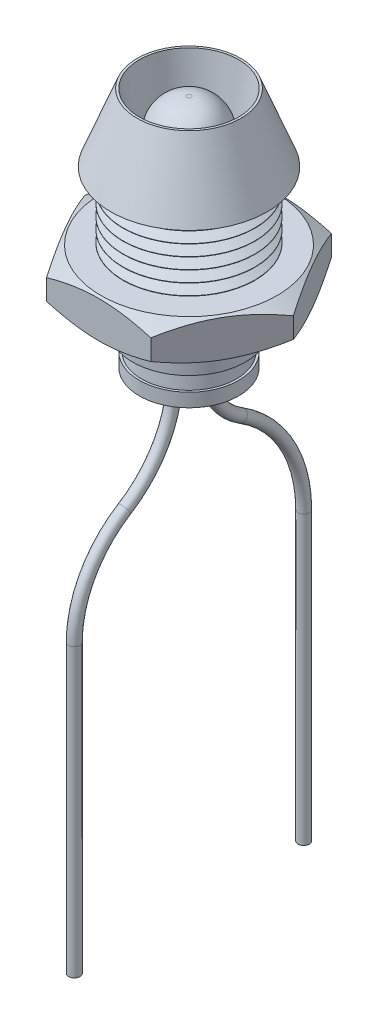
SolidWorks part; units mm, degrees
other "Nut"
other "Tip"
other "Wire LED"
other "LED Light"
other "Plastic Insert"
material "Plain Carbon Steel"
ref_plane "Front Plane" through (0, 0, 0) normal (0, 0, 1) x (1, 0, 0)
ref_plane "Top Plane" through (0, 0, 0) normal (0, 1, 0) x (1, 0, 0)
ref_plane "Right Plane" through (0, 0, 0) normal (1, 0, 0) x (0, 0, -1)
sketch "Sketch1" plane through (0, 0, 0) normal (0, 0, 1) x (1, 0, 0)
  line L0 (0, 0) -> (0, 9.25)
  line L1 (0, 0) -> (2.5, 0)
  line L2 (2.92, 0.6) -> (2.92, 6.25)
  line L3 (0, 9.25) -> (2.3, 9.25)
  line L4 (2.92, 6.25) -> (3.47, 6.25)
  line L5 (3.47, 6.25) -> (2.3, 9.25)
  line L6 (2.5, 0) -> (2.5, 0.6)
  line L7 (2.5, 0.6) -> (2.92, 0.6)
  dimension "D1" = 9.25
  dimension "D2" = 2.92
  dimension "D3" = 2.3
  dimension "D4" = 3.47
  dimension "D5" = 3
  dimension "D6" = 2.5
  dimension "D7" = 6.25
  dimension "D8" = 0.6
revolve "Revolve1" add sketch "Sketch1" angle 360 about L0
sketch "Sketch6" plane through (0, 0, 0) normal (0, 0, 1) x (1, 0, 0)
  line L0 (0, 0) -> (0, 9.25)
  line L1 (2.3, 9.25) -> (-2.3, 9.25) construction
  line L2 (0, 0) -> (2.05, 0)
  line L3 (2.05, 0) -> (2.05, 5.8)
  line L4 (2.05, 5.8) -> (1.75, 5.8)
  line L5 (1.75, 5.8) -> (2.2, 9.25)
  line L6 (2.2, 9.25) -> (0, 9.25)
  line L7 (1.75, 5.8) -> (0, 5.8) construction
  dimension "D1" = 2.05
  dimension "D2" = 5.8
  dimension "D3" = 2.2
  dimension "D4" = 1.75
revolve "Cut-Revolve2" cut sketch "Sketch6" angle 360 about L0
sketch "Sketch5" plane through (0, 0, 0) normal (0, 0, 1) x (1, 0, 0)
  line L0 (0, 0) -> (0, 0.6) construction
  line L1 (-2.5, 0.6) -> (2.5, 0.6) construction
  line L2 (0, 0.6) -> (2.5, 0.6) construction
  line L3 (2.5, 0.6) -> (2.933, 0.6) construction
  line L4 (2.933, 0.6) -> (3.433, 0.6) construction
  line L5 (3.433, 0.85) -> (3.433, 0.35)
  line L6 (2.933, 0.85) -> (2.933, 0.35) construction
  line L7 (3.433, 0.85) -> (2.933, 0.85)
  line L8 (2.933, 0.85) -> (2.5, 0.6)
  line L9 (2.5, 0.6) -> (2.933, 0.35)
  line L10 (2.933, 0.35) -> (3.433, 0.35)
  line L11 (2.5, 0) -> (2.5, 0.6) construction
  point P12 (2.959, 0.6)
  point P13 (2.5, 0.6)
  dimension "D1" = 0.5
  dimension "D2" = 60
revolve "Cut-Revolve1" cut sketch "Sketch5" angle 360 about L0
pattern_linear "LPattern1" count 11 spacing 0.5 along (0, 1, 0) of "Cut-Revolve1"
ref_plane "GAP DISTANCE" through (0, 3.25, 0) normal (0, -1, 0) x (-1, 0, 0)
sketch "Sketch7" plane through (0, 3.25, 0) normal (0, -1, 0) x (-1, 0, 0)
  line L1 (-4.6188, 0) -> (-2.3094, -4)
  line L2 (-2.3094, -4) -> (2.3094, -4)
  line L3 (2.3094, -4) -> (4.6188, 0)
  line L4 (4.6188, 0) -> (2.3094, 4)
  line L5 (2.3094, 4) -> (-2.3094, 4)
  line L6 (-2.3094, 4) -> (-4.6188, 0)
  circle A0 centre (0, 0) radius 4 construction
  circle A1 centre (0, 0) radius 2.6
  dimension "D1" = 8
  dimension "D2" = 5.2
extrude "Boss-Extrude1" add sketch "Sketch7" along normal blind 1.74 separate body
sketch "Sketch8" plane through (0, 0, 0) normal (0, 0, 1) x (1, 0, 0)
  line L0 (0, 0) -> (0, 1.51) construction
  line L1 (2.3094, 1.51) -> (-2.3094, 1.51) construction
  line L2 (0, 1.51) -> (0, 3.25) construction
  line L3 (2.3094, 3.25) -> (-2.3094, 3.25) construction
  line L4 (0, 3.25) -> (3.9, 3.25) construction
  line L5 (4.6188, 3.25) -> (2.3094, 3.25) construction
  line L6 (3.9, 3.25) -> (3.9, 1.51) construction
  line L7 (4.6188, 1.51) -> (2.3094, 1.51) construction
  line L8 (3.9, 1.51) -> (0, 1.51) construction
  line L9 (3.9, 3.25) -> (4.6188, 3.25)
  line L10 (4.6188, 3.25) -> (4.6188, 2.835)
  line L11 (4.6188, 1.51) -> (4.6188, 3.25) construction
  line L12 (4.6188, 2.835) -> (3.9, 3.25)
  line L13 (3.9, 1.51) -> (4.6188, 1.51)
  line L14 (4.6188, 1.51) -> (4.6188, 1.925)
  line L15 (4.6188, 1.925) -> (3.9, 1.51)
  point P5 (4.6188, 2.6837)
  point P23 (4.6188, 1.441)
  dimension "D1" = 3.9
  dimension "D2" = 30
revolve "Cut-Revolve3" cut sketch "Sketch8" angle 360 about L2
sketch "Sketch11" plane through (0, 0, 0) normal (0, 0, 1) x (1, 0, 0)
  line L0 (0, 3.55) -> (0, -1.45)
  line L1 (0, -1.45) -> (2.2, -1.45)
  line L2 (0, 3.55) -> (1.75, 3.55)
  line L4 (2.2, -1.45) -> (2.2, -0.85)
  line L5 (2.2, -0.85) -> (2.1, -0.85)
  line L6 (2.1, -0.85) -> (1.75, 3.55)
  line L7 (0, 3.55) -> (0, 9.25) construction
  line L8 (2.3, 9.25) -> (-2.3, 9.25) construction
  dimension "D1" = 0.1
  dimension "D2" = 2.2
  dimension "D3" = 1.75
  dimension "D4" = 5
  dimension "D5" = 0.6
  dimension "D6" = 10.7
revolve "Revolve2" add sketch "Sketch11" angle 360 about L7
sketch "Sketch12" plane through (0, 3.55, 0) normal (0, 1, 0) x (1, 0, 0)
  circle A0 centre (0, 0) radius 1.5
  dimension "D1" = 3
extrude "Cut-Extrude5" cut sketch "Sketch12" against normal offset from surface (4.4 mm away) 0.6 up to face at (0, -1.45, -2.2)
sketch "Sketch13" plane through (0, -0.85, 0) normal (0, 1, 0) x (1, 0, 0)
  line L0 (0, 0.635) -> (0, -0.635) construction
  line L2 (-0.4, 1.035) -> (0.4, 1.035)
  line L3 (-0.4, 1.035) -> (-0.4, 0.235)
  line L4 (-0.4, 0.235) -> (0.4, 0.235)
  line L5 (0.4, 1.035) -> (0.4, 0.235)
  line L6 (-0.4, 1.035) -> (0.4, 0.235) construction
  line L7 (-0.4, 0.235) -> (0.4, 1.035) construction
  line L8 (-0.4, -0.235) -> (0.4, -0.235)
  line L9 (-0.4, -0.235) -> (-0.4, -1.035)
  line L10 (-0.4, -1.035) -> (0.4, -1.035)
  line L11 (0.4, -0.235) -> (0.4, -1.035)
  line L12 (-0.4, -0.235) -> (0.4, -1.035) construction
  line L13 (-0.4, -1.035) -> (0.4, -0.235) construction
  dimension "D1" = 1.27
  dimension "D2" = 0.8
extrude "Cut-Extrude6" cut sketch "Sketch13" against normal up to surface (0.6 mm away) up to face at (0, -1.45, -2.2)
sketch "Sketch14" plane through (0, -1.45, 0) normal (0, -1, 0) x (1, 0, 0)
  line L0 (0, 1.035) -> (0, 0.235) construction
  line L1 (-0.4, 1.035) -> (0.4, 1.035) construction
  line L2 (0.4, 0.235) -> (-0.4, 0.235) construction
  line L3 (0, -0.235) -> (0, -1.035) construction
  line L4 (-0.4, -0.235) -> (0.4, -0.235) construction
  line L5 (0.4, -1.035) -> (-0.4, -1.035) construction
  circle A0 centre (0, -0.635) radius 0.6
  circle A1 centre (0, 0.635) radius 0.6
  dimension "D1" = 1.2
extrude "Cut-Extrude7" cut sketch "Sketch14" against normal blind 0.1
sketch "Sketch21" plane through (0, -1.45, 0) normal (0, -1, 0) x (1, 0, 0)
  line L0 (0, 0) -> (0, 1.4) construction
  line L1 (0, 0) -> (0, -2) construction
  line L2 (-1.25, -2) -> (1.25, -2) construction
  line L3 (-1.25, 1.4) -> (1.25, 1.4) construction
  text T0 "A" font "Calibri" height 0.6
  text T1 "C" font "Calibri" height 0.6
  dimension "D1" = 2
  dimension "D2" = 1.4
extrude "Cut-Extrude9" cut sketch "Sketch21" against normal blind 0.01
sketch "Sketch15" plane through (0, 0, 0) normal (0, 0, 1) x (1, 0, 0)
  line L0 (0, 0) -> (0, 3.55) construction
  line L1 (1.75, 3.55) -> (-1.75, 3.55) construction
  line L2 (0, 3.55) -> (0, 8.95)
  line L3 (0, 3.55) -> (1.89, 3.55)
  line L4 (1.89, 3.55) -> (1.89, 4.75)
  line L5 (1.89, 4.75) -> (1.5, 4.75)
  line L6 (1.5, 4.75) -> (1.5, 5.05)
  line L8 (0.1, 8.95) -> (0, 8.95)
  line L9 (1.5, 5.05) -> (1.5, 7.55) construction
  line L10 (1.5, 7.55) -> (1.5, 8.95) construction
  line L11 (1.5, 8.95) -> (0.1, 8.95) construction
  line L12 (1.5, 7.55) -> (1.47, 7.55) construction
  line L13 (1.5, 4.75) -> (0, 4.75) construction
  line L14 (1.47, 7.55) -> (0, 7.55) construction
  arc A0 (1.5, 5.05) -> (1.4676, 7.6464) centre (-102.6817, 5.05) ccw
  arc A1 (0.1, 8.95) -> (1.4616, 7.7345) centre (0.1, 7.5797) cw
  arc A2 (1.4616, 7.7345) -> (1.4676, 7.6464) centre (0.468, 7.6215) cw
  dimension "D1" = 1.5
  dimension "D7" = 0.1
  dimension "D9" = 1
  dimension "D2" = 1.89
  dimension "D3" = 1.2
  dimension "D4" = 5.4
  dimension "D5" = 1.47
  dimension "D6" = 1.5
  dimension "D8" = 4
revolve "Revolve3" add sketch "Sketch15" angle 360 about L2
sketch "Sketch17" plane through (0, 4.75, 0) normal (0, 1, 0) x (1, 0, 0)
  line L0 (0, 0) -> (0, 1.53) construction
  line L1 (-1.1096, 1.53) -> (1.1096, 1.53)
  circle A0 centre (0, 0) radius 1.89 construction
  arc A1 (1.1096, 1.53) -> (-1.1096, 1.53) centre (0, 0) ccw
  point P3 (0.707, 2.52)
  point P4 (0, 1.9022)
  point P5 (0, 2.1105)
  point P7 (0, 1.5432)
  point P9 (1.1905, 1.5275)
  dimension "D1" = 1.53
extrude "Cut-Extrude8" cut sketch "Sketch17" against normal up to surface (1.2 mm away) up to face at (0, 3.55, -1.89)
sketch "Sketch Wire Path" plane through (0, 0, 0) normal (1, 0, 0) x (0, 0, -1)
  line L0 (0, 0) -> (0, 3.55) construction
  line L1 (-0.635, -1.45) -> (0.635, -1.45) construction
  line L2 (-1.89, 3.55) -> (1.53, 3.55) construction
  line L3 (0, 3.55) -> (0, 4.75) construction
  line L4 (1.53, 4.75) -> (-1.89, 4.75) construction
  line L5 (-0.635, 4.15) -> (0, 4.15)
  line L6 (-0.635, 4.15) -> (-0.635, -1.45)
  line L7 (0.635, 4.15) -> (0.635, -1.45)
  line L8 (-0.635, -1.45) -> (-0.635, -5.45) construction
  line L9 (-0.635, -5.45) -> (-2.8575, -5.45) construction
  line L10 (-2.8575, -5.45) -> (-5.08, -5.45) construction
  line L11 (-5.08, -5.45) -> (-5.08, -9.45) construction
  line L12 (0.635, -1.45) -> (0.635, -4.45) construction
  line L13 (0.635, -4.45) -> (2.3019, -4.45) construction
  line L14 (2.3019, -4.45) -> (5.08, -4.45) construction
  line L15 (5.08, -4.45) -> (5.08, -9.45) construction
  line L16 (-5.08, -9.45) -> (-5.08, -22.1586)
  line L17 (5.08, -9.45) -> (5.08, -22.1586)
  line L18 (0, 0) -> (0, -22.1586) construction
  line L19 (-5.08, -22.1586) -> (0, -22.1586) construction
  line L20 (0, -22.1586) -> (5.08, -22.1586) construction
  line L21 (0, 4.15) -> (0.635, 4.15)
  line L22 (-2.2, -1.45) -> (2.2, -1.45) construction
  arc A0 (-0.635, -1.45) -> (-2.8575, -5.45) centre (-5.3458, -1.45) cw
  arc A1 (-2.8575, -5.45) -> (-5.08, -9.45) centre (-0.3692, -9.45) ccw
  arc A2 (0.635, -1.45) -> (2.3019, -4.45) centre (4.1681, -1.45) ccw
  arc A3 (2.3019, -4.45) -> (5.08, -9.45) centre (-0.8085, -9.45) cw
  point P23 (0, -1.45)
  dimension "D2" = 57
  dimension "D3" = 8
  dimension "D1" = 1.27
  dimension "D4" = 5.08
  dimension "D5" = 5.08
  dimension "D7" = 8
  dimension "D8" = 4
  dimension "D9" = 5
sketch "Sketch Wire Profile" plane through (0, 0, 0) normal (0, 0, 1) x (1, 0, 0)
  line L0 (0, 3.55) -> (0, 4.75) construction
  circle A0 centre (0, 4.15) radius 0.25
  dimension "D1" = 0.5
sweep "ADJUST LED WIRES" add profiles "Sketch Wire Profile" path "Sketch Wire Path"
